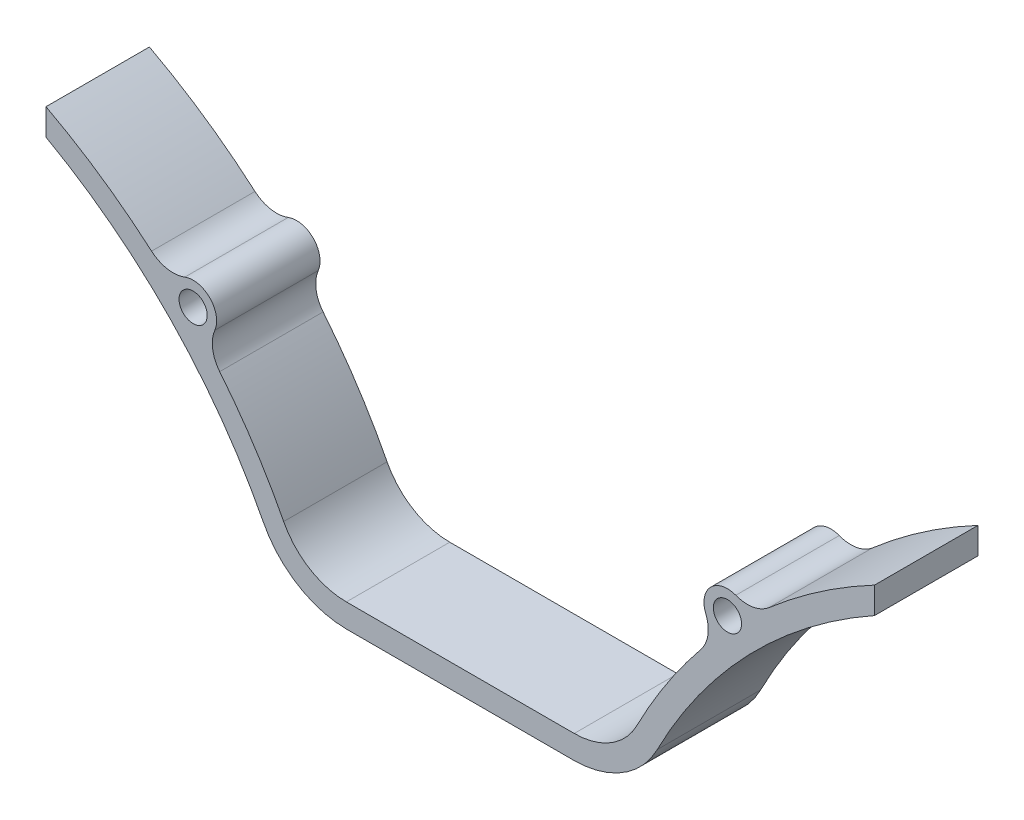
SolidWorks part; units mm, degrees
ref_plane "Plano frontal" through (0, 0, 0) normal (0, 0, 1) x (1, 0, 0)
ref_plane "Plano superior" through (0, 0, 0) normal (0, 1, 0) x (1, 0, 0)
ref_plane "Plano direito" through (0, 0, 0) normal (1, 0, 0) x (0, 0, -1)
sketch "Esboço1" plane through (0, 0, 0) normal (0, 0, 1) x (1, 0, 0)
  line L0 (-88.1314, -3.7131) -> (-88.1314, -9.3321)
  line L3 (-24.2376, -63) -> (24.2376, -63)
  line L24 (88.1314, -3.7131) -> (88.1314, -9.3321)
  line L54 (-24.1062, -68) -> (24.1062, -68)
  arc A0 (24.1062, -68) -> (41.8901, -57.1507) centre (24.1062, -48) ccw
  arc A1 (-41.8901, -57.1507) -> (-24.1062, -68) centre (-24.1062, -48) ccw
  arc A2 (-51.1834, -34.0488) -> (-52.2174, -26.9468) centre (-45.7528, -29.6318) cw
  arc A3 (41.8901, -57.1507) -> (88.1314, -9.3321) centre (144.147, -109.7674) cw
  arc A5 (-50.4763, -34.9265) -> (-51.1834, -34.0488) centre (-144.2784, -109.7674) ccw
  arc A6 (-37.5755, -54.863) -> (-50.4763, -34.9265) centre (-144.2784, -109.7674) ccw
  arc A8 (-24.2376, -63) -> (-37.5755, -54.863) centre (-24.2376, -48) cw
  arc A12 (-65.6729, -19.0968) -> (-58.6068, -20.3533) centre (-61.0875, -13.8076) ccw
  arc A16 (-65.6729, -19.0968) -> (-88.1314, -3.7131) centre (-144.2784, -109.7674) ccw
  arc A18 (-58.6068, -20.3533) -> (-52.2174, -26.9468) centre (-56.8349, -25.0288) cw
  circle A20 centre (-56.8349, -25.0288) radius 3
  arc A24 (58.6068, -20.3533) -> (52.2174, -26.9468) centre (56.8349, -25.0288) ccw
  arc A26 (65.6729, -19.0968) -> (88.1314, -3.7131) centre (144.2784, -109.7674) cw
  arc A28 (65.6729, -19.0968) -> (58.6068, -20.3533) centre (61.0875, -13.8076) cw
  circle A33 centre (56.8349, -25.0288) radius 3
  arc A34 (24.2376, -63) -> (37.5755, -54.863) centre (24.2376, -48) ccw
  arc A35 (37.5755, -54.863) -> (50.4763, -34.9265) centre (144.2784, -109.7674) cw
  arc A40 (50.4763, -34.9265) -> (51.1834, -34.0488) centre (144.2784, -109.7674) cw
  arc A41 (51.1834, -34.0488) -> (52.2174, -26.9468) centre (45.7528, -29.6318) ccw
  arc A43 (-41.8901, -57.1507) -> (-88.1314, -9.3321) centre (-144.147, -109.7674) ccw
extrude "Ressalto-extrusão1" add sketch "Esboço1" along normal blind 22
